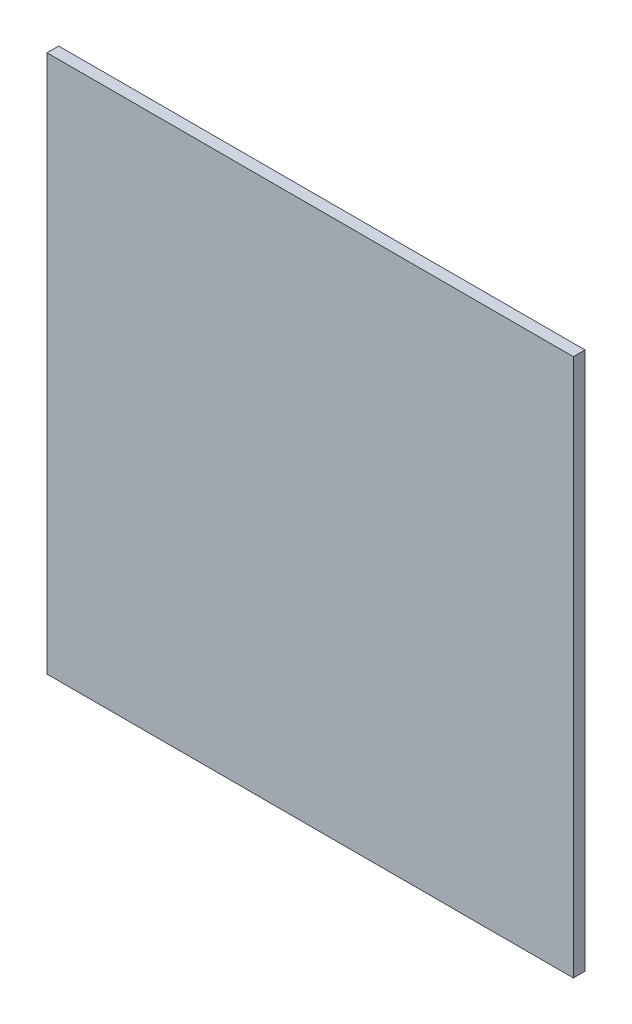
SolidWorks part; units mm, degrees
ref_plane "Front Plane" through (0, 0, 0) normal (0, 0, 1) x (1, 0, 0)
ref_plane "Top Plane" through (0, 0, 0) normal (0, 1, 0) x (1, 0, 0)
ref_plane "Right Plane" through (0, 0, 0) normal (1, 0, 0) x (0, 0, -1)
sketch "Sketch1" plane through (0, 0, 0) normal (0, 0, 1) x (1, 0, 0)
  line L1 (71.4375, -73.025) -> (-71.4375, -73.025)
  line L2 (71.4375, -73.025) -> (71.4375, 73.025)
  line L3 (71.4375, 73.025) -> (-71.4375, 73.025)
  line L4 (-71.4375, -73.025) -> (-71.4375, 73.025)
  line L5 (71.4375, -73.025) -> (-71.4375, 73.025) construction
  line L6 (71.4375, 73.025) -> (-71.4375, -73.025) construction
  point P0 (0, 0)
  dimension "D1" = 142.875
  dimension "D2" = 146.05
extrude "Boss-Extrude1" add sketch "Sketch1" along normal blind 3.175
